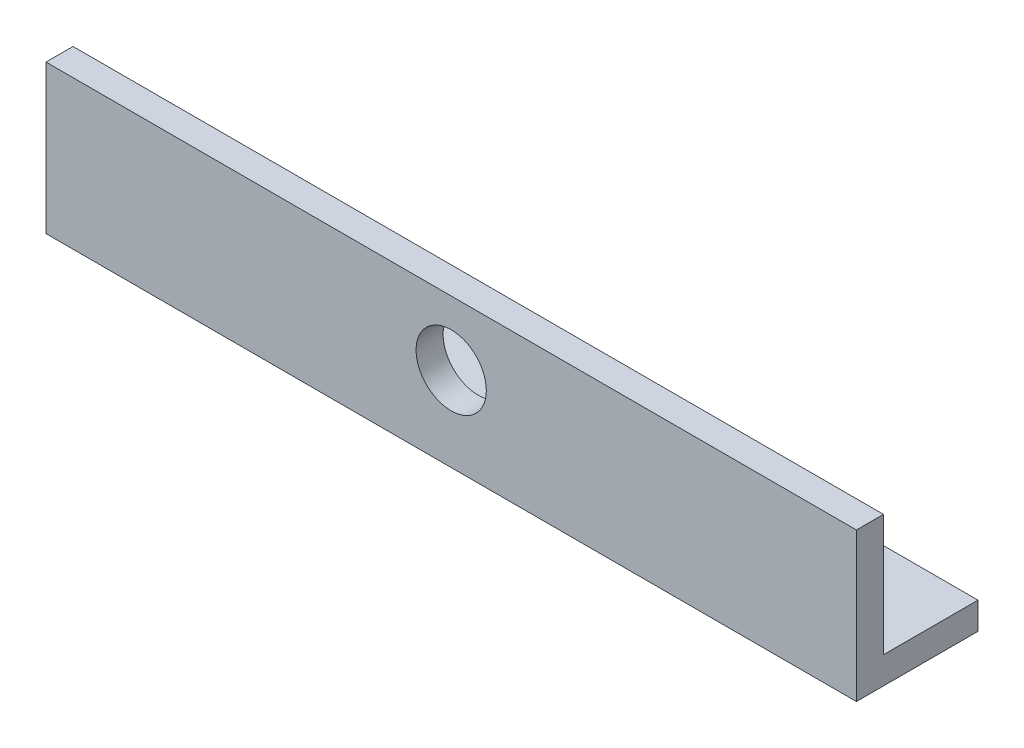
SolidWorks part; units mm, degrees
ref_plane "Front Plane" through (0, 0, 0) normal (0, 0, 1) x (1, 0, 0)
ref_plane "Top Plane" through (0, 0, 0) normal (0, 1, 0) x (1, 0, 0)
ref_plane "Right Plane" through (0, 0, 0) normal (1, 0, 0) x (0, 0, -1)
sketch "Sketch1" plane through (0, 0, 0) normal (1, 0, 0) x (0, 0, -1)
  line L0 (0, 23.8095) -> (0, -26.1905)
  line L1 (0, -26.1905) -> (40, -26.1905)
  dimension "D1" = 40
  dimension "D2" = 50
extrude "Extrude-Thin1" add sketch "Sketch1" along normal mid plane 300 thin thin type mid plane wall 10
sketch "Sketch2" plane through (0, 0, 5) normal (0, 0, 1) x (1, 0, 0)
  circle A0 centre (0, 0) radius 13
extrude "Cut-Extrude1" cut sketch "Sketch2" against normal through all
